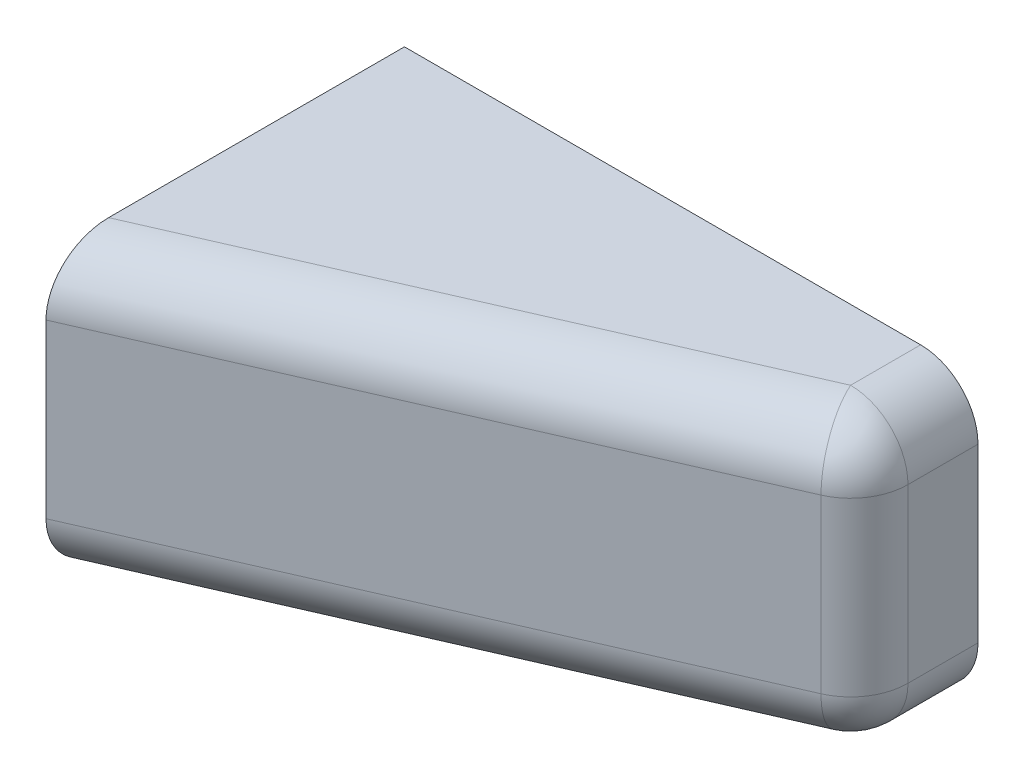
SolidWorks part; units mm, degrees
ref_plane "Front Plane" through (0, 0, 0) normal (0, 0, 1) x (1, 0, 0)
ref_plane "Top Plane" through (0, 0, 0) normal (0, 1, 0) x (1, 0, 0)
ref_plane "Right Plane" through (0, 0, 0) normal (1, 0, 0) x (0, 0, -1)
sketch "Sketch1" plane through (0, 0, 0) normal (0, 0, 1) x (1, 0, 0)
  line L0 (0, 0) -> (40, 0)
  line L1 (40, 0) -> (40, 20)
  line L2 (40, 20) -> (0, 20)
  line L3 (0, 20) -> (0, 0)
  line L4 (0, 10) -> (13, 10) construction
  line L5 (13, 10) -> (34, 10) construction
  circle A0 centre (13, 10) radius 1.6
  circle A1 centre (34, 10) radius 1.6
  dimension "D3" = 10
  dimension "D1" = 40
  dimension "D2" = 20
extrude "Boss-Extrude1" add sketch "Sketch1" along normal blind 5
sketch "Sketch3" plane through (0, 0, 5) normal (0, 0, 1) x (1, 0, 0)
  line L0 (0, 12.75) -> (0, 7.25) construction
  line L1 (0, 20) -> (0, 0) construction
  line L2 (34, 12.75) -> (34, 7.25) construction
  line L3 (34, 7.25) -> (35.5877, 7.25) construction
  line L4 (34, 10) -> (36.3816, 8.625) construction
  line L5 (36.3816, 8.625) -> (34.8509, 5.9739) construction
  line L6 (35.5877, 7.25) -> (36.3816, 8.625)
  line L7 (34, 10) -> (38.0826, 10) construction
  line L8 (36.3816, 8.625) -> (37.1754, 10)
  line L9 (35.5877, 7.25) -> (0, 7.25)
  line L10 (0, 7.25) -> (0, 0)
  line L11 (0, 0) -> (40, 0)
  line L12 (40, 0) -> (40, 20)
  line L13 (40, 0) -> (40, 20) construction
  line L14 (36.3816, 11.375) -> (34.8509, 14.0261) construction
  line L15 (34, 10) -> (36.3816, 11.375) construction
  line L16 (34, 12.75) -> (35.5877, 12.75) construction
  line L17 (0, 20) -> (40, 20)
  line L18 (0, 12.75) -> (0, 20)
  line L19 (35.5877, 12.75) -> (0, 12.75)
  line L20 (36.3816, 11.375) -> (37.1754, 10)
  line L21 (35.5877, 12.75) -> (36.3816, 11.375)
  point P24 (0, 10)
  point P25 (40, 10)
  dimension "D1" = 2.75
extrude "Boss-Extrude2" add sketch "Sketch3" along normal blind 2.5
sketch "Sketch4" plane through (0, 20, 0) normal (0, 1, 0) x (1, 0, 0)
  line L0 (40, -7.5) -> (0, -25)
  line L1 (0, -25) -> (0, -7.5)
  line L2 (0, -7.5) -> (40, -7.5)
  dimension "D1" = 17.5
extrude "Boss-Extrude3" add sketch "Sketch4" against normal through all
sketch "Sketch6" plane through (0, 0, 0) normal (-1, 0, 0) x (0, 0, 1)
  line L0 (0, 10) -> (0, 6)
  line L1 (0, 20) -> (0, 0) construction
  line L2 (0, 6) -> (14, 6)
  line L3 (14, 6) -> (14, 10) construction
  line L4 (14, 14) -> (0, 14)
  line L5 (0, 14) -> (0, 10)
  arc A0 (14, 6) -> (14, 14) centre (14, 10) ccw
  dimension "D1" = 14
extrude "Cut-Extrude1" cut sketch "Sketch6" against normal blind 2.5
sketch "Sketch7" plane through (0, 0, 0) normal (0, 0, -1) x (-1, 0, 0)
  line L0 (-2.5, 14) -> (-2.5, 16)
  line L1 (-2.5, 16) -> (-9.5, 16)
  line L2 (-2.5, 6) -> (-2.5, 4)
  line L3 (-2.5, 4) -> (-9.5, 4)
  line L4 (-9.5, 4) -> (-9.5, 16)
  line L5 (-2.5, 14) -> (-2.5, 6)
  dimension "D1" = 12
  dimension "D2" = 7
  dimension "D3" = 2
extrude "Cut-Extrude2" cut sketch "Sketch7" against normal blind 20 contours L1 L4 L3 L2 L5 L0
fillet "Fillet1" radius 4 5 edges at (40, 0, 3.75) (40, 20, 3.75) (40, 10, 7.5) (20, 20, 16.25) (20, 0, 16.25)
chamfer "Chamfer1" distance 1 angle 45 12 edges at (9.5, 12.75, 6.25) (9.5, 10, 5) (9.5, 7.25, 6.25) (9.5, 10, 7.5) (2.5, 10, 18) (2.5, 6, 7) (2.5, 5, 0) (2.5, 14, 7) (2.5, 15, 0) (6, 4, 0) (9.5, 10, 0) (6, 16, 0)
